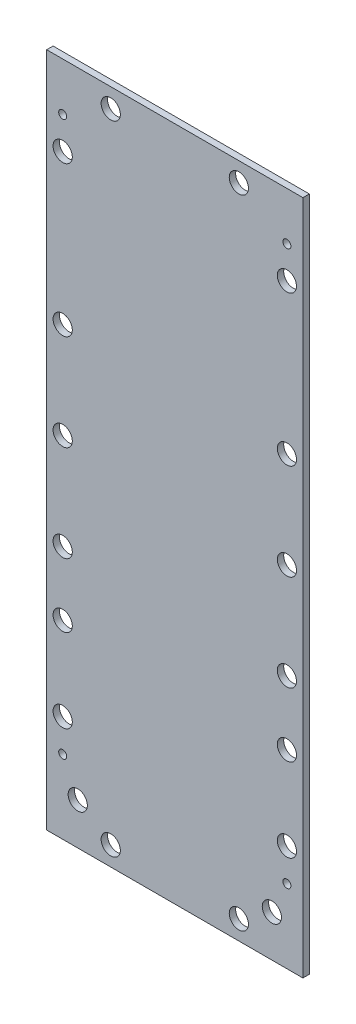
SolidWorks part; units mm, degrees
ref_plane "Front Plane" through (0, 0, 0) normal (0, 0, 1) x (1, 0, 0)
ref_plane "Top Plane" through (0, 0, 0) normal (0, 1, 0) x (1, 0, 0)
ref_plane "Right Plane" through (0, 0, 0) normal (1, 0, 0) x (0, 0, -1)
sketch "Sketch2" plane through (0, 0, 0) normal (0, 0, 1) x (1, 0, 0)
  line L0 (0, 0) -> (0, 211)
  line L1 (0, 211) -> (80, 211)
  line L2 (80, 211) -> (80, 0)
  line L3 (80, 0) -> (0, 0)
extrude "Boss-Extrude1" add sketch "Sketch2" along normal blind 2
sketch "Sketch3" plane through (0, 0, 0) normal (0, 0, -1) x (-1, 0, 0)
  line L0 (-80, 196) -> (0, 196) construction
  line L1 (-80, 0) -> (-80, 211) construction
  line L2 (0, 211) -> (0, 0) construction
  line L3 (-80, 23) -> (0, 23) construction
  line L4 (-75, 211) -> (-75, 0) construction
  line L5 (-80, 211) -> (0, 211) construction
  line L6 (0, 0) -> (-80, 0) construction
  line L7 (-5, 211) -> (-5, 0) construction
  line L8 (-40, 211) -> (-40, 0) construction
  dimension "D1" = 23
  dimension "D2" = 15
  dimension "D3" = 35
  dimension "70" = 70
hole_wizard "M3x0.5 Tapped Hole1" positions "Sketch4" profile "Sketch6" tap size "M3x0.5" standard "ANSI Metric"
sketch "Sketch4" plane through (0, 0, 0) normal (0, 0, -1) x (-1, 0, 0)
  line L0 (-80, 196) -> (0, 196) construction
  line L1 (-75, 211) -> (-75, 0) construction
  line L2 (-5, 211) -> (-5, 0) construction
  line L3 (-80, 23) -> (0, 23) construction
  point P0 (-75, 196)
  point P6 (-5, 196)
  point P10 (-75, 23)
  point P14 (-5, 23)
sketch "Sketch6" plane through (75, 196, 0) normal (1, 0, 0) x (0, 1, 0)
  line L0 (0, 0) -> (0, 10.7511)
  line L1 (0, 10.7511) -> (1.25, 10)
  line L2 (1.25, 10) -> (1.25, 0)
  line L5 (1.25, 0) -> (0, 0)
  line L10 (0, 10.7511) -> (-1.25, 10) construction
  line L11 (0, -6.35) -> (0, 107.95) construction
  dimension "Tap Drill Dia." = 2.5
  dimension "Tap Drill Depth" = 10
  dimension "Drill Angle" = 118
sketch "Sketch7" plane through (0, 0, 0) normal (0, 0, -1) x (-1, 0, 0)
  line L0 (-75, 211) -> (-75, 0) construction
  line L1 (-80, 211) -> (0, 211) construction
  line L2 (0, 0) -> (-80, 0) construction
  line L3 (-5, 211) -> (-5, 0) construction
  line L4 (-40, 211) -> (-40, 0) construction
  line L5 (-80, 0) -> (-80, 211) construction
  line L6 (0, 211) -> (0, 0) construction
  circle A0 centre (-75, 186) radius 3
  circle A1 centre (-75, 139.2) radius 3
  circle A2 centre (-75, 109.2) radius 3
  circle A3 centre (-75, 79.2) radius 3
  circle A4 centre (-75, 59.2) radius 3
  circle A5 centre (-75, 33.2) radius 3
  circle A6 centre (-5, 186) radius 3
  circle A7 centre (-5, 139.2) radius 3
  circle A8 centre (-5, 109.2) radius 3
  circle A9 centre (-5, 79.2) radius 3
  circle A10 centre (-5, 59.2) radius 3
  circle A11 centre (-5, 33.2) radius 3
  circle A12 centre (-70.3, 13) radius 3
  circle A13 centre (-60, 205) radius 3
  circle A14 centre (-20, 205) radius 3
  circle A15 centre (-60, 6) radius 3
  circle A16 centre (-20, 6) radius 3
  circle A17 centre (-9.7, 13) radius 3
  dimension "D4" = 6
  dimension "D10" = 40
  dimension "D1" = 70
  dimension "D2" = 35
  dimension "D3" = 25
  dimension "D5" = 46.8
  dimension "D6" = 30
  dimension "D7" = 30
  dimension "D8" = 20
  dimension "D9" = 26
  dimension "D11" = 20
  dimension "D12" = 6
  dimension "D13" = 6
  dimension "D14" = 9.7
  dimension "D15" = 9.7
  dimension "D16" = 13
extrude "Cut-Extrude1" cut sketch "Sketch7" against normal up to surface (2 mm away) up to face at (73.75, 196, 2)
